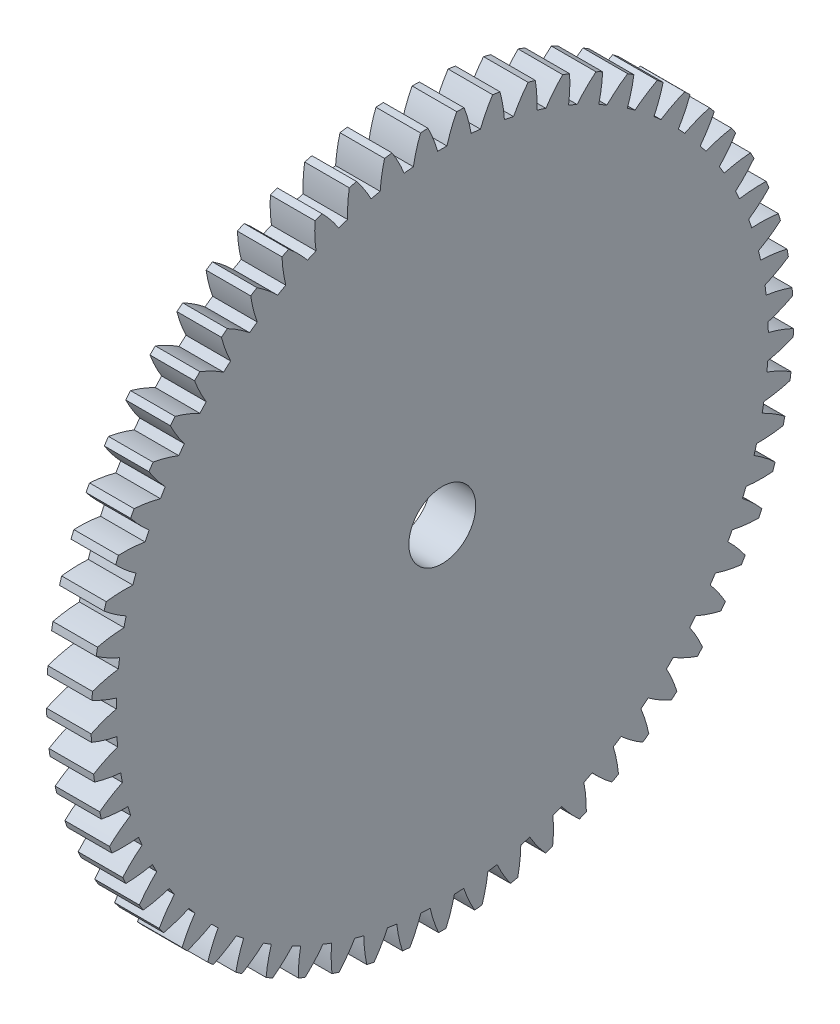
SolidWorks part; units mm, degrees
ref_plane "Plane1" through (0, 0, 0) normal (0, 0, 1) x (1, 0, 0)
ref_plane "Plane2" through (0, 0, 0) normal (0, 1, 0) x (1, 0, 0)
ref_plane "Plane3" through (0, 0, 0) normal (1, 0, 0) x (0, 0, -1)
sketch "HoldingSke" plane through (0, 0, 0) normal (0, 1, 0) x (1, 0, 0)
  line L0 (0, 0) -> (1.9392, -3.4985)
  line L1 (-15, 0) -> (100, 0) construction
  line L2 (0, 0) -> (-2.1039, 2.3779)
  line L3 (0, 0) -> (-11.863, 4.5341)
  line L4 (0, 0) -> (4.1868, 7.5532)
  line L5 (0, 0) -> (-46.8476, -17.4728)
  line L6 (0, 0) -> (-0.829, -0.5593)
  line L7 (-2.1039, 2.3779) -> (8.6586, 51.2059)
  line L8 (-76.2, 54.61) -> (-76, 54.61)
  line L9 (-71.009, 38.7566) -> (-53.1078, 45.2721)
  line L10 (-76.2, 71.12) -> (104.1128, 71.12)
  line L11 (0, 0) -> (-1, 0)
  line L12 (-76.2, 101.6) -> (-76.192, 101.6)
  line L13 (24.9733, 27.94) -> (52.9518, 28.4284)
  line L14 (24.9733, 27.94) -> (24.9743, 27.94)
  line L15 (24.9733, 27.94) -> (100.4006, 29.5858)
  line L16 (-63.627, -0.25) -> (-12.827, -0.25)
  circle A0 centre (0, 0) radius 0.75
  circle A1 centre (0, 0) radius 7.3115
  circle A2 centre (0, 0) radius 37.5
  circle A3 centre (0, 0) radius 0.75
  dimension "MHD" = 14.623
  dimension "Hub_dia" = 75
  dimension "Bore" = 1.5
  dimension "MBD" = 1.5
  dimension "Num_teeth" = 61
  dimension "Pitch" = 4
  dimension "Overall_len" = 50
  dimension "Show_teeth" = 61
  dimension "Thickness" = 1
  dimension "OAL" = 50.0001
  dimension "T_dim" = 0.2
  dimension "Ap" = 20
  dimension "H" = 19.05
  dimension "Pitch_radius" = 180.3128
  dimension "Width" = 1
  dimension "Backlash" = 0.008
  dimension "Addendum_fac" = 1
  dimension "Dedendum_fac" = 1.25
  dimension "Clearance_fac" = 0.25
  dimension "Dedendum_add" = 0.001
  dimension "Module" = 0.25
sketch "BasProSke" plane through (0, 0, 0) normal (0, 1, 0) x (1, 0, 0)
  line L0 (-10, 0) -> (60, 0) construction
  line L1 (0, 0) -> (0, 7.875)
  line L2 (0, 0) -> (1, 0)
  line L3 (1, 0) -> (1, 7.875)
  line L4 (1, 7.875) -> (0, 7.875)
  dimension "Thickness" = 1
  dimension "Diameter" = 15.75
revolve "Base-Revolve" add sketch "BasProSke" angle 360 about L0
sketch "TooCutSke" plane through (0, 0, 0) normal (1, 0, 0) x (0, 0, -1)
  line L1 (0, 0) -> (0, 107) construction
  line L2 (0, 0) -> (-0.2103, 7.6221) construction
  line L3 (0, 0) -> (-0.7848, 15.2254) construction
  line L4 (-0.2103, 7.6221) -> (-0.3924, 7.6127) construction
  arc A0 (0.1047, 7.3108) -> (-0.1047, 7.3108) centre (0, 0) ccw
  arc A1 (0.3347, 7.8933) -> (-0.3347, 7.8933) centre (0, 0) ccw
  circle A2 centre (0, 0) radius 7.625 construction
  circle A3 centre (0, 0) radius 7.1652 construction
  arc A4 (-0.1047, 7.3108) -> (-0.3347, 7.8933) centre (-3.0415, 6.4876) ccw
  arc A5 (0.3347, 7.8933) -> (0.1047, 7.3108) centre (3.0415, 6.4876) ccw
  dimension "Root_dia" = 14.623
  dimension "Overcut_dia" = 15.8008
  dimension "Pitch_dia" = 15.25
  dimension "Base_dia" = 14.3303
  dimension "Flank_rad" = 3.05
  dimension "Half_ang" = 2.951
  dimension "Half_CT" = 0.1823
extrude "ToothCut" cut sketch "TooCutSke" along normal through all
fillet "Breaks" [suppressed] radius 0.005
fillet "RootFillets" [suppressed] radius 0.0635
pattern_circular "TeethCuts" count 61 every 5.902 about axis through (-10, 0, 0) along (1, 0, 0) of "ToothCut", "RootFillets", "Breaks"
sketch "HubNeaOneSke" plane through (0, 0, 0) normal (-1, 0, 0) x (0, 0, 1)
  circle A0 centre (0, 0) radius 7.3115
  dimension "Diameter" = 14.623
extrude "HubNearOne" [suppressed] add sketch "HubNeaOneSke" along normal blind 49.0001
sketch "HubNeaBotSke" plane through (0, 0, 0) normal (-1, 0, 0) x (0, 0, 1)
  circle A0 centre (0, 0) radius 7.3115
  dimension "Diameter" = 14.623
extrude "HubNearBoth" [suppressed] add sketch "HubNeaBotSke" along normal blind 24.5
ref_plane "FarPln" through (1, 0, 0) normal (1, 0, 0) x (0, 0, -1)
sketch "HubFarSke" plane through (1, 0, 0) normal (1, 0, 0) x (0, 0, -1)
  circle A0 centre (0, 0) radius 7.3115
  dimension "Diameter" = 14.623
extrude "HubFar" [suppressed] add sketch "HubFarSke" along normal blind 24.5
sketch "BorSke" plane through (0, 0, 0) normal (1, 0, 0) x (0, 0, -1)
  circle A0 centre (0, 0) radius 0.75
  dimension "Diameter" = 1.5
extrude "Bore" cut sketch "BorSke" along normal mid plane 100.0001
sketch "KeySke" plane through (0, 0, 0) normal (1, 0, 0) x (0, 0, -1)
  line L0 (-0.3, 0) -> (-0.3, 0.95)
  line L1 (-0.3, 0.95) -> (0.3, 0.95)
  line L2 (0.3, 0.95) -> (0.3, 0)
  line L3 (0, 0) -> (0, 34) construction
  line L4 (-0.3, 0) -> (0.3, 0)
  dimension "Offset" = 0.95
  dimension "Width" = 0.6
extrude "Keyway" [suppressed] cut sketch "KeySke" along normal mid plane 100.0001
pattern_circular "Keyway2" [suppressed] count 2 every 90 about axis through (-10, 0, 0) along (1, 0, 0)
equation "' \"Module@HoldingSke\" = 6.35"
equation "' \"Num_teeth@HoldingSke\" = 12"
equation "' \"Ap@HoldingSke\" =  20"
equation "' \"Ap@HoldingSke\" = 20"
equation "' \"Width@HoldingSke\" = 0.5 * 25.4"
equation "' \"Hub_dia@HoldingSke\"= 1 * 25.4"
equation "' \"Hub_dia@HoldingSke\" = 1 * 25.4"
equation "' \"Overall_len@HoldingSke\" = 1.0 * 25.4"
equation "' \"Bore@HoldingSke\" = 0.75 * 25.4"
equation "' \"T_dim@HoldingSke\" = 0.1 * 25.4"
equation "' \"Width@KeySke\" = 0.25 * 25.4"
equation "' \"Show_teeth@HoldingSke\" = 13"
equation "' \"Backlash@HoldingSke\" = 0.009 * 25.4"
equation "' \"Addendum_fac@HoldingSke\" = 1.0"
equation "' \"Dedendum_fac@HoldingSke\" = 1.25"
equation "' \"Dedendum_add@HoldingSke\" = 0.00005 * 25.4"
equation "' \"Clearance_fac@HoldingSke\" = 0.25"
equation "\"Pitch@HoldingSke\" = 1 / \"Module@HoldingSke\""
equation "\"Overcut_dia@TooCutSke\" = (\"Num_teeth@HoldingSke\" + 2 * \"Addendum_fac@HoldingSke\") / \"Pitch@HoldingSke\" + 0.002 * 25.4"
equation "\"Pitch_dia@TooCutSke\" = \"Num_teeth@HoldingSke\" / \"Pitch@HoldingSke\""
equation "\"Base_dia@TooCutSke\" = \"Num_teeth@HoldingSke\" / \"Pitch@HoldingSke\" * cos((\"Ap@HoldingSke\"  * 3.14159265 / 180))"
equation "\"Root_dia@TooCutSke\" = (\"Num_teeth@HoldingSke\" + 2) / \"Pitch@HoldingSke\" - 2 * (\"Addendum_fac@HoldingSke\" + \"Dedendum_fac@HoldingSke\") / \"Pitch@HoldingSke\" - \"Dedendum_add@HoldingSke\" * 2"
equation "\"Half_ang@TooCutSke\" = 180 / \"Num_teeth@HoldingSke\""
equation "\"Half_CT@TooCutSke\" = \"Num_teeth@HoldingSke\" / \"Pitch@HoldingSke\" * sin((3.14159265 / 2 / \"Num_teeth@HoldingSke\")) / 2 - 7 * \"Backlash@HoldingSke\" / 4"
equation "\"Flank_rad@TooCutSke\" = \"Num_teeth@HoldingSke\" / \"Pitch@HoldingSke\" / 5"
equation "\"Radius@RootFillets\" = \"Clearance_fac@HoldingSke\" / \"Pitch@HoldingSke\" + \"Dedendum_add@HoldingSke\""
equation "\"Break_rad@Breaks\" = 0.02 / \"Pitch@HoldingSke\""
equation "\"Thickness@HoldingSke\" = \"Width@HoldingSke\""
equation "\"OAL@HoldingSke\" = \"Thickness@HoldingSke\""
equation "\"MHD@HoldingSke\" = (\"Num_teeth@HoldingSke\" + 2) / \"Pitch@HoldingSke\" - 2 * (\"Addendum_fac@HoldingSke\" + \"Dedendum_fac@HoldingSke\")  / \"Pitch@HoldingSke\" - \"Dedendum_add@HoldingSke\" * 2"
equation "\"MBD@HoldingSke\" = (\"Num_teeth@HoldingSke\" + 2) / \"Pitch@HoldingSke\" - 2 * (\"Addendum_fac@HoldingSke\" + \"Dedendum_fac@HoldingSke\")  / \"Pitch@HoldingSke\" - \"Dedendum_add@HoldingSke\" * 2 - 0.002 * 25.4"
equation "\"MHD@HoldingSke\" = ((sgn( \"MHD@HoldingSke\" - \"Hub_dia@HoldingSke\" )-1)*( \"MHD@HoldingSke\" - \"Hub_dia@HoldingSke\" ))/-2+ \"Hub_dia@HoldingSke\""
equation "\"MBD@HoldingSke\" = ((sgn( \"MBD@HoldingSke\" - \"Bore@HoldingSke\" )-1)*( \"MBD@HoldingSke\" - \"Bore@HoldingSke\" ))/-2+ \"Bore@HoldingSke\""
equation "\"OAL@HoldingSke\" = ((sgn( \"OAL@HoldingSke\" - \"Overall_len@HoldingSke\" )+1)*( \"OAL@HoldingSke\" - \"Overall_len@HoldingSke\" ))/2 + \"Overall_len@HoldingSke\" + 0.000002 * 25.4"
equation "\"Num_teeth@TeethCuts\" = int( \"Show_teeth@HoldingSke\" ) + 1"
equation "\"Num_teeth@TeethCuts\" = ((sgn( \"Num_teeth@TeethCuts\" - \"Num_teeth@HoldingSke\" )-1)*( \"Num_teeth@TeethCuts\" - \"Num_teeth@HoldingSke\" ))/-2+ \"Num_teeth@HoldingSke\""
equation "\"Num_teeth@TeethCuts\" = ((sgn( \"Num_teeth@TeethCuts\" - 2.0)+1)*( \"Num_teeth@TeethCuts\" - 2.0))/2 +2.0"
equation "\"Angle@TeethCuts\" = 360.0 / \"Num_teeth@HoldingSke\""
equation "\"Diameter@BasProSke\" = (\"Num_teeth@HoldingSke\" + 2 * \"Addendum_fac@HoldingSke\") / \"Pitch@HoldingSke\""
equation "\"Thickness@BasProSke\"  = \"Thickness@HoldingSke\""
equation "' \"Fillet_rad@BasProSke\" =  \"Thickness@HoldingSke\" * 0.05"
equation "' \"Fillet_rad@BasProSke\" = \"Thickness@HoldingSke\" * 0.05"
equation "\"MHD@HoldingSke\" = ((sgn( \"MHD@HoldingSke\" - \"Root_dia@TooCutSke\" )-1)*( \"MHD@HoldingSke\" - \"Root_dia@TooCutSke\" ))/-2+ \"Root_dia@TooCutSke\""
equation "\"Diameter@HubNeaOneSke\" = \"MHD@HoldingSke\""
equation "\"Length@HubNearOne\" = \"OAL@HoldingSke\" - \"Thickness@BasProSke\""
equation "\"Diameter@HubNeaBotSke\" = \"MHD@HoldingSke\""
equation "\"Length@HubNearBoth\" = ( \"OAL@HoldingSke\" - \"Thickness@BasProSke\" ) / 2.0"
equation "\"Thickness@FarPln\" = \"Thickness@BasProSke\""
equation "\"Diameter@HubFarSke\" = \"MHD@HoldingSke\""
equation "\"Length@HubFar\" = ( \"OAL@HoldingSke\" - \"Thickness@BasProSke\" ) / 2.0"
equation "\"Diameter@BorSke\" = \"MBD@HoldingSke\""
equation "\"D1@Bore\" = \"OAL@HoldingSke\" * 2.0"
equation "\"D1@Keyway\" = \"OAL@HoldingSke\" * 2.0"
equation "\"Offset@KeySke\" = \"T_dim@HoldingSke\" + \"MBD@HoldingSke\" / 2.0"
